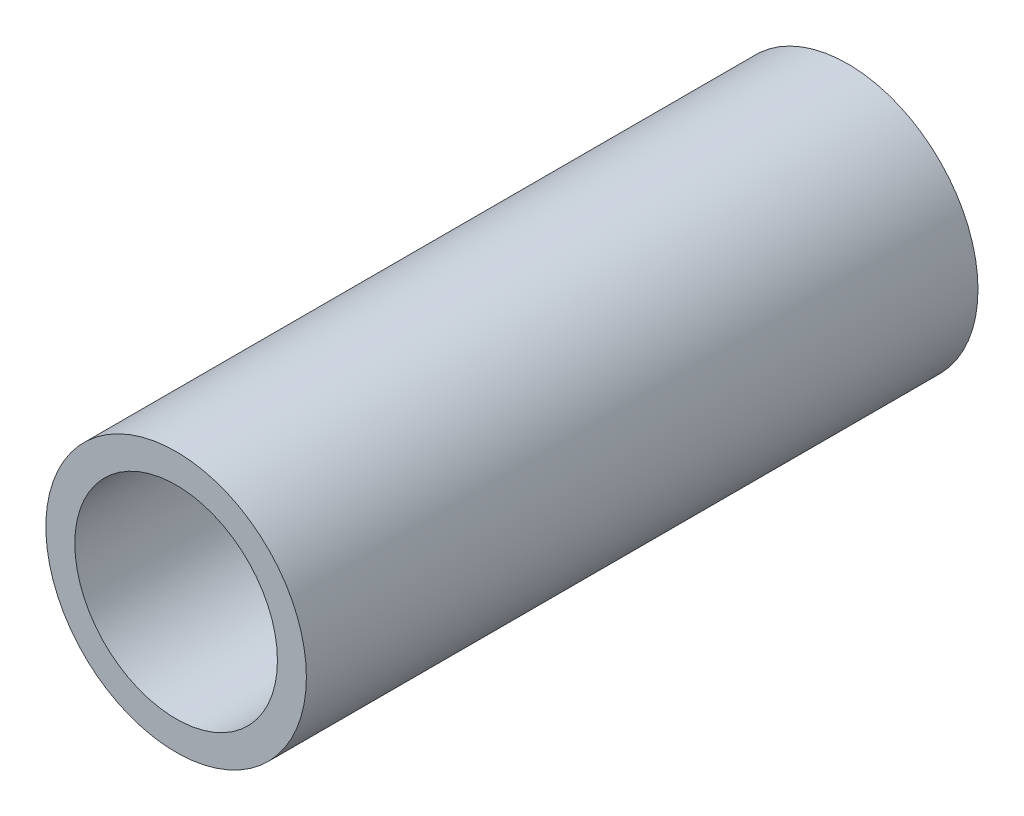
SolidWorks part; units mm, degrees
ref_plane "Plan de face" through (0, 0, 0) normal (0, 0, 1) x (1, 0, 0)
ref_plane "Plan de dessus" through (0, 0, 0) normal (0, 1, 0) x (1, 0, 0)
ref_plane "Plan de droite" through (0, 0, 0) normal (1, 0, 0) x (0, 0, -1)
sketch "Esquisse1" plane through (0, 0, 0) normal (0, 0, 1) x (1, 0, 0)
  circle A0 centre (0, 0) radius 4.375
  circle A1 centre (0, 0) radius 5.625
extrude "Extrusion1" add sketch "Esquisse1" along normal blind 29
